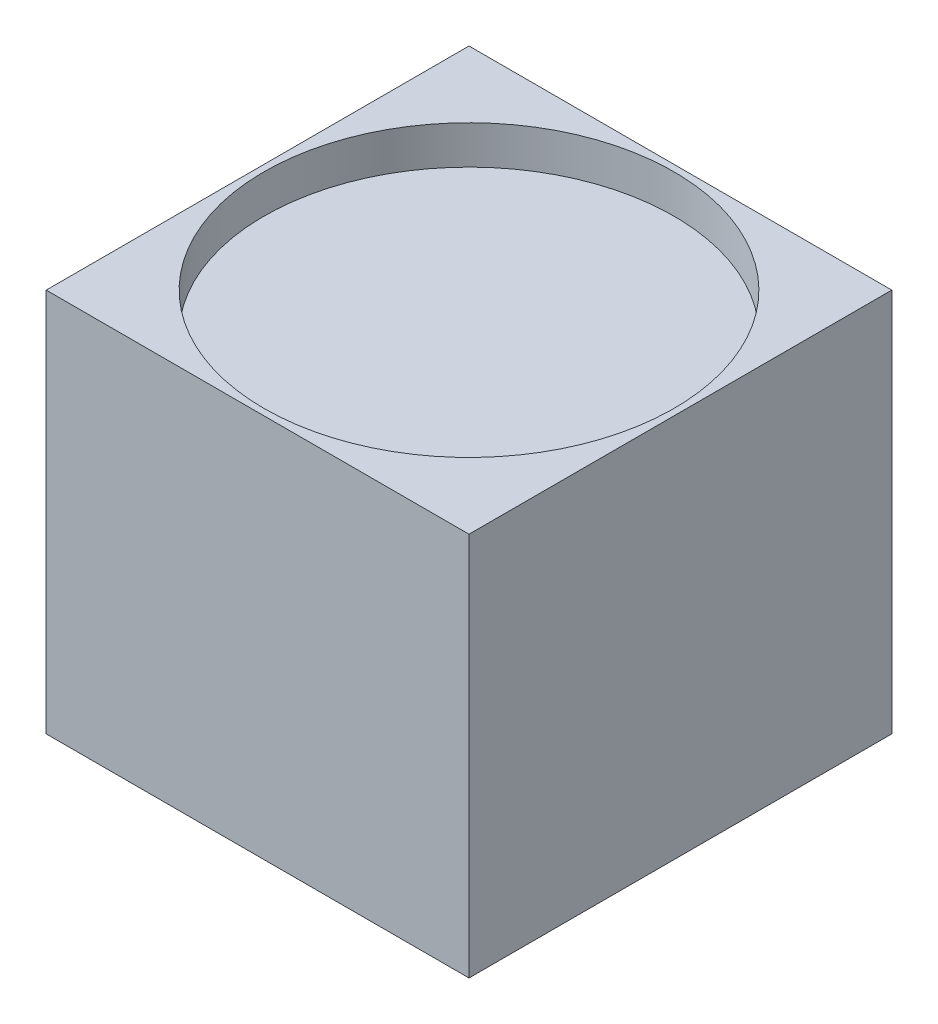
SolidWorks part; units mm, degrees
ref_plane "Front Plane" through (0, 0, 0) normal (0, 0, 1) x (1, 0, 0)
ref_plane "Top Plane" through (0, 0, 0) normal (0, 1, 0) x (1, 0, 0)
ref_plane "Right Plane" through (0, 0, 0) normal (1, 0, 0) x (0, 0, -1)
sketch "Sketch1" plane through (0, 0, 0) normal (0, 1, 0) x (1, 0, 0)
  line L1 (-16.5, -16.5) -> (16.5, -16.5)
  line L2 (-16.5, -16.5) -> (-16.5, 16.5)
  line L3 (-16.5, 16.5) -> (16.5, 16.5)
  line L4 (16.5, -16.5) -> (16.5, 16.5)
  line L5 (-16.5, -16.5) -> (16.5, 16.5) construction
  line L6 (-16.5, 16.5) -> (16.5, -16.5) construction
  point P0 (0, 0)
  dimension "D1" = 33
  dimension "D2" = 33
extrude "Boss-Extrude1" add sketch "Sketch1" along normal blind 30
sketch "Sketch2" plane through (0, 30, 0) normal (0, 1, 0) x (1, 0, 0)
  circle A0 centre (0, 0) radius 16
  dimension "D1" = 32
extrude "Cut-Extrude1" cut sketch "Sketch2" against normal blind 3
sketch "Sketch3" plane through (0, 0, 0) normal (0, -1, 0) x (1, 0, 0)
  circle A0 centre (0, 0) radius 1
  dimension "D1" = 2
extrude "Cut-Extrude2" cut sketch "Sketch3" against normal blind 2
fillet "Fillet1" radius 1 1 edges at (0, 2, -1)
